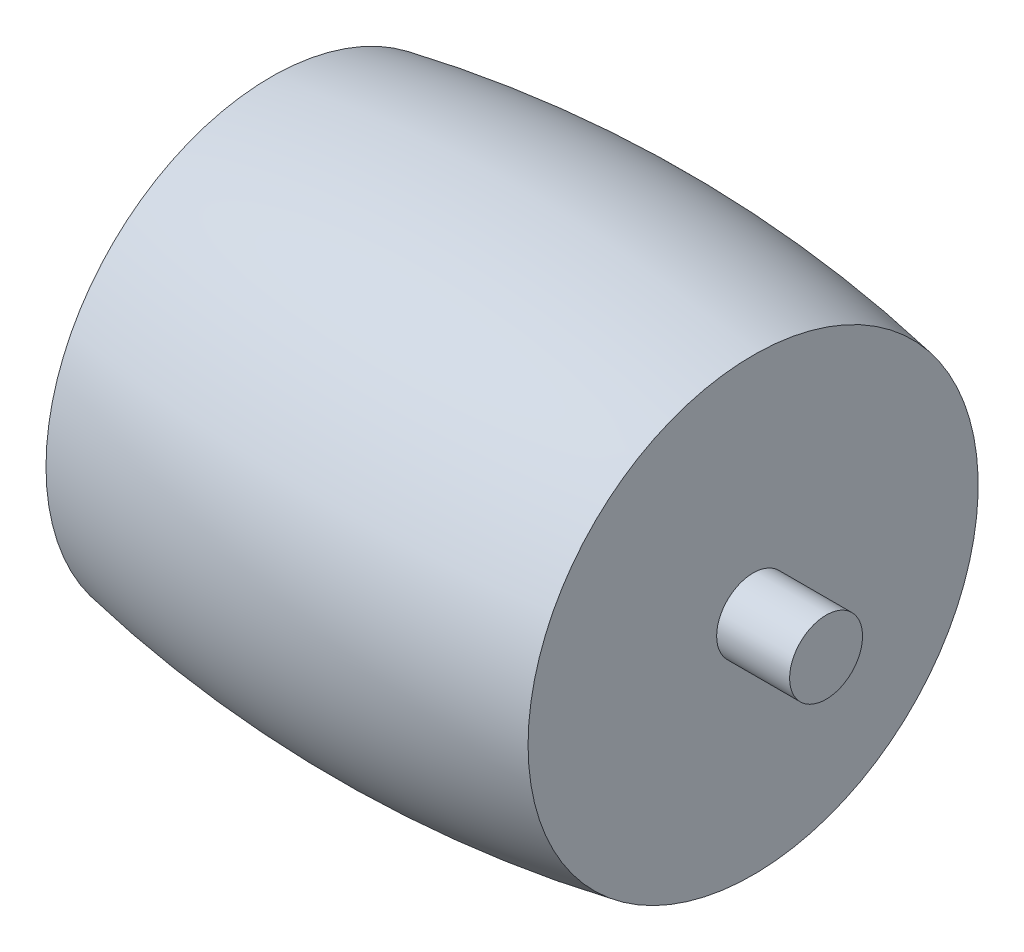
SolidWorks part; units mm, degrees
material "POLYURETHANE (11671)"
ref_plane "Front Plane" through (0, 0, 0) normal (0, 0, 1) x (1, 0, 0)
ref_plane "Top Plane" through (0, 0, 0) normal (0, 1, 0) x (1, 0, 0)
ref_plane "Right Plane" through (0, 0, 0) normal (1, 0, 0) x (0, 0, -1)
sketch "Sketch1" plane through (0, 0, 0) normal (0, 0, 1) x (1, 0, 0)
  line L1 (0, 50) -> (0, 40.5) construction
  line L2 (9.25, 49.1369) -> (9.25, 41.9)
  line L3 (-9.25, 40.5) -> (-12.05, 40.5)
  line L4 (-9.25, 40.5) -> (9.25, 40.5)
  line L7 (-12.05, 41.9) -> (-12.05, 40.5)
  line L8 (9.25, 41.9) -> (12.05, 41.9)
  line L9 (-9.25, 41.9) -> (-12.05, 41.9)
  line L10 (9.25, 40.5) -> (12.05, 40.5)
  line L11 (12.05, 41.9) -> (12.05, 40.5)
  line L12 (-9.25, 49.1369) -> (-9.25, 41.9)
  arc A0 (9.25, 49.1369) -> (-9.25, 49.1369) centre (0, 0) ccw
  dimension "D1" = 100
  dimension "D2" = 18.5
  dimension "D3" = 9.5
  dimension "D4" = 2.8
  dimension "D5" = 1.4
revolve "Revolve1" add sketch "Sketch1" angle 360 about L4
scale "Scale1" scale about origin uniform scaling yes scale factor 0.630435
